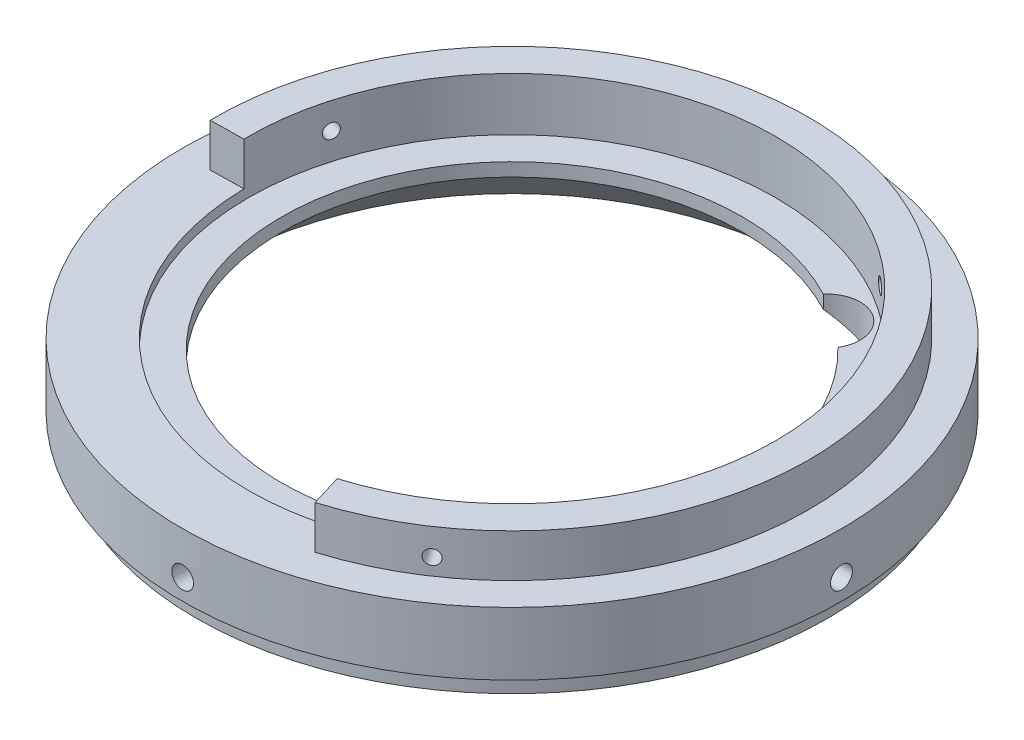
SolidWorks part; units mm, degrees
ref_plane "Front Plane" through (0, 0, 0) normal (0, 0, 1) x (1, 0, 0)
ref_plane "Top Plane" through (0, 0, 0) normal (0, 1, 0) x (1, 0, 0)
ref_plane "Right Plane" through (0, 0, 0) normal (1, 0, 0) x (0, 0, -1)
sketch "Sketch2" plane through (0, 0, 0) normal (0, 0, 1) x (1, 0, 0)
  line L0 (47.675, 0) -> (0, 0) construction
  line L1 (0, 0) -> (0, 12.7) construction
  line L2 (49.7, 12.7) -> (49.7, 3.2004)
  line L3 (49.7, 3.2004) -> (47.675, 3.2004)
  line L4 (47.675, 3.2004) -> (47.675, 0)
  line L5 (0, 12.7) -> (49.7, 12.7) construction
  line L6 (49.7, 12.7) -> (44.75, 12.7)
  line L11 (44.75, 12.7) -> (44.75, 19.2)
  line L12 (44.75, 19.2) -> (39.75, 19.2)
  line L13 (39.75, 19.2) -> (39.75, 11.2)
  line L14 (39.75, 11.2) -> (34.75, 11.2)
  line L15 (34.75, 11.2) -> (34.75, 9.2)
  line L16 (34.75, 9.2) -> (44.7, 0)
  line L17 (44.7, 0) -> (47.675, 0)
  dimension "D1" = 49.7
  dimension "D2" = 2.025
  dimension "D3" = 9.4996
  dimension "D4" = 12.7
  dimension "D5" = 39.75
  dimension "D6" = 5
  dimension "D7" = 5
  dimension "D8" = 1.5
  dimension "D9" = 5
  dimension "D10" = 8
  dimension "D11" = 2
revolve "Revolve1" add sketch "Sketch2" angle 360 about L1
ref_axis "Axis1" through (0, 13.335, 0) along (0, -1, 0)
sketch "Sketch5" plane through (0, 0, 0) normal (0, 0, 1) x (1, 0, 0)
  line L0 (0, 13.335) -> (0, -0.635) construction
  line L1 (0, 12.7) -> (0, 0) construction
  line L2 (-44.7, 0) -> (44.7, 0) construction
  line L3 (49.7, 12.7) -> (-49.7, 12.7) construction
  circle A0 centre (0, 6.35) radius 1.6425
  point P10 (0, 6.35)
  dimension "D1" = 3.285
extrude "Cut-Extrude1" cut sketch "Sketch5" against normal through all
ref_plane "Plane1" through (0, 0, 0) normal (-0.5878, 0, 0.809) x (0.809, 0, 0.5878)
sketch "Sketch6" plane through (0, 0, 0) normal (-0.5878, 0, 0.809) x (0.809, 0, 0.5878)
  line L0 (0, 19.2) -> (0, 11.2) construction
  line L2 (39.75, 19.2) -> (-39.75, 19.2) construction
  line L5 (0, 13.335) -> (0, -0.635) construction
  line L6 (39.75, 11.2) -> (-39.75, 11.2) construction
  circle A0 centre (0, 15.2) radius 1.095
  dimension "D1" = 2.19
extrude "Cut-Extrude2" cut sketch "Sketch6" against normal through all
pattern_circular "CirPattern1" count 4 over 360 about axis through (0, 13.335, 0) along (0, -1, 0) of "Cut-Extrude1"
sketch "Sketch7" plane through (0, 19.2, 0) normal (0, 1, 0) x (-1, 0, 0)
  line L0 (44.7433, 0.7731) -> (39.7441, 0.6867)
  line L1 (-13.0912, 42.7923) -> (-11.6285, 38.0111)
  line L2 (0, 0) -> (26.3034, 36.2035) construction
  line L3 (6.2161, -4.5162) -> (-6.2161, 4.5162) construction
  arc A0 (39.7441, 0.6867) -> (-11.6285, 38.0111) centre (0, 0) ccw
  circle A1 centre (0, 0) radius 39.75 construction
  arc A2 (-13.0912, 42.7923) -> (44.7433, 0.7731) centre (0, 0) cw
  circle A3 centre (0, 0) radius 44.75 construction
  dimension "D1" = 63.5
extrude "Cut-Extrude3" cut sketch "Sketch7" against normal up to surface (6.5 mm away) up to face at (0, 12.7, -44.75)
pattern_circular "CirPattern2" count 2 every 110 about axis through (0, 13.335, 0) along (0, -1, 0) of "Cut-Extrude2"
pattern_circular "CirPattern3" count 2 every 110 about axis through (0, 13.335, 0) along (0, -1, 0) of "Cut-Extrude2"
sketch "Sketch8" plane through (0, 11.2, 0) normal (0, 1, 0) x (1, 0, 0)
  line L0 (19.9847, 27.5066) -> (0, 0) construction
  line L1 (-6.2161, 4.5162) -> (6.2161, -4.5162) construction
  line L2 (16.1816, 30.7525) -> (24.247, 24.8927)
  arc A0 (16.1816, 30.7525) -> (24.247, 24.8927) centre (19.9847, 27.5066) cw
  circle A1 centre (0, 0) radius 34.75 construction
  dimension "D1" = 5
  dimension "D2" = 34
extrude "Cut-Extrude5" cut sketch "Sketch8" against normal up to surface (2 mm away)
